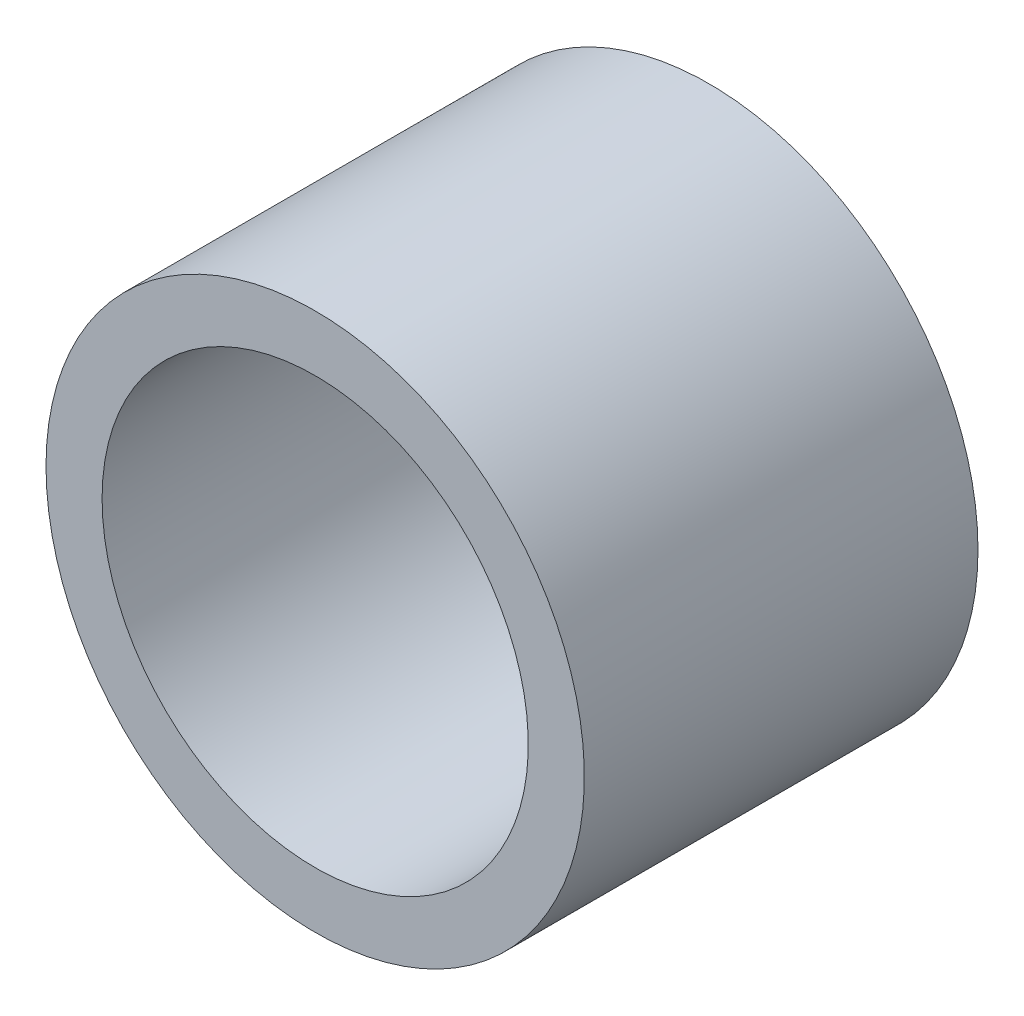
SolidWorks part; units mm, degrees
ref_plane "Alzado" through (0, 0, 0) normal (0, 0, 1) x (1, 0, 0)
ref_plane "Planta" through (0, 0, 0) normal (0, 1, 0) x (1, 0, 0)
ref_plane "Vista lateral" through (0, 0, 0) normal (1, 0, 0) x (0, 0, -1)
sketch "Croquis1" plane through (0, 0, 0) normal (0, 0, 1) x (1, 0, 0)
  circle A3 centre (24.8351, -26) radius 9.5
  circle A5 centre (24.8351, -26) radius 12
extrude "Saliente-Extruir1" add sketch "Croquis1" along normal up to surface (17.5486 mm away)
